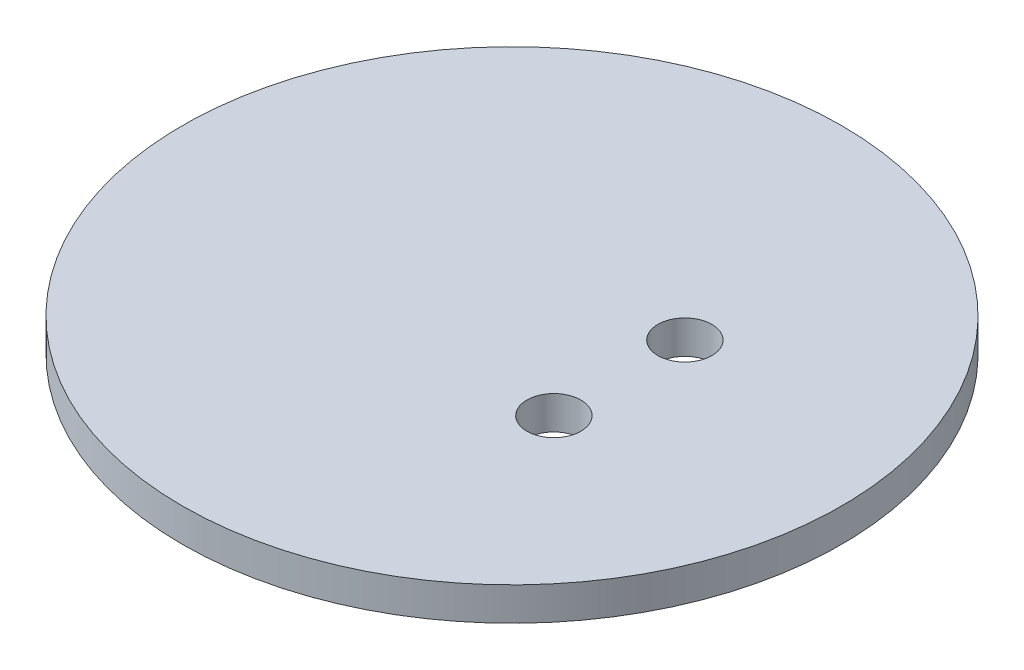
SolidWorks part; units mm, degrees
ref_plane "Front" through (0, 0, 0) normal (0, 0, 1) x (1, 0, 0)
ref_plane "Top" through (0, 0, 0) normal (0, 1, 0) x (1, 0, 0)
ref_plane "Right" through (0, 0, 0) normal (1, 0, 0) x (0, 0, -1)
sketch "Sketch1" plane through (0, 0, 0) normal (0, 1, 0) x (1, 0, 0)
  circle A0 centre (0, 0) radius 7.925
  dimension "D1" = 15.85
extrude "Boss-Extrude1" add sketch "Sketch1" along normal blind 0.8
sketch "Sketch3" plane through (0, 0.8, 0) normal (0, 1, 0) x (1, 0, 0)
  line L0 (2.5826, 1.575) -> (2.5826, -1.575) construction
  circle A0 centre (2.5826, 1.575) radius 0.65
  circle A1 centre (2.5826, -1.575) radius 0.65
  circle A2 centre (0, 0) radius 7.925 construction
  point P4 (2.5826, 0)
  dimension "D1" = 1.3
  dimension "D2" = 1.85
  dimension "D3" = 4.25
extrude "Cut-Extrude1" cut sketch "Sketch3" against normal blind 0.9
sketch "Sketch5" plane through (0, 0.8, 0) normal (0, 1, 0) x (1, 0, 0)
  line L0 (-0.925, 8.3) -> (-0.925, -8.3) construction
  line L1 (0.575, 8.3) -> (-2.425, 8.3)
  line L2 (0.575, 8.3) -> (0.575, -8.3)
  line L3 (0.575, -8.3) -> (-2.425, -8.3)
  line L4 (-2.425, 8.3) -> (-2.425, -8.3)
  line L5 (-2.425, 0) -> (0.575, 0) construction
  circle A1 centre (0, 0) radius 7.925 construction
  dimension "D3" = 8.5
  dimension "D1" = 3
  dimension "D2" = 16.6
